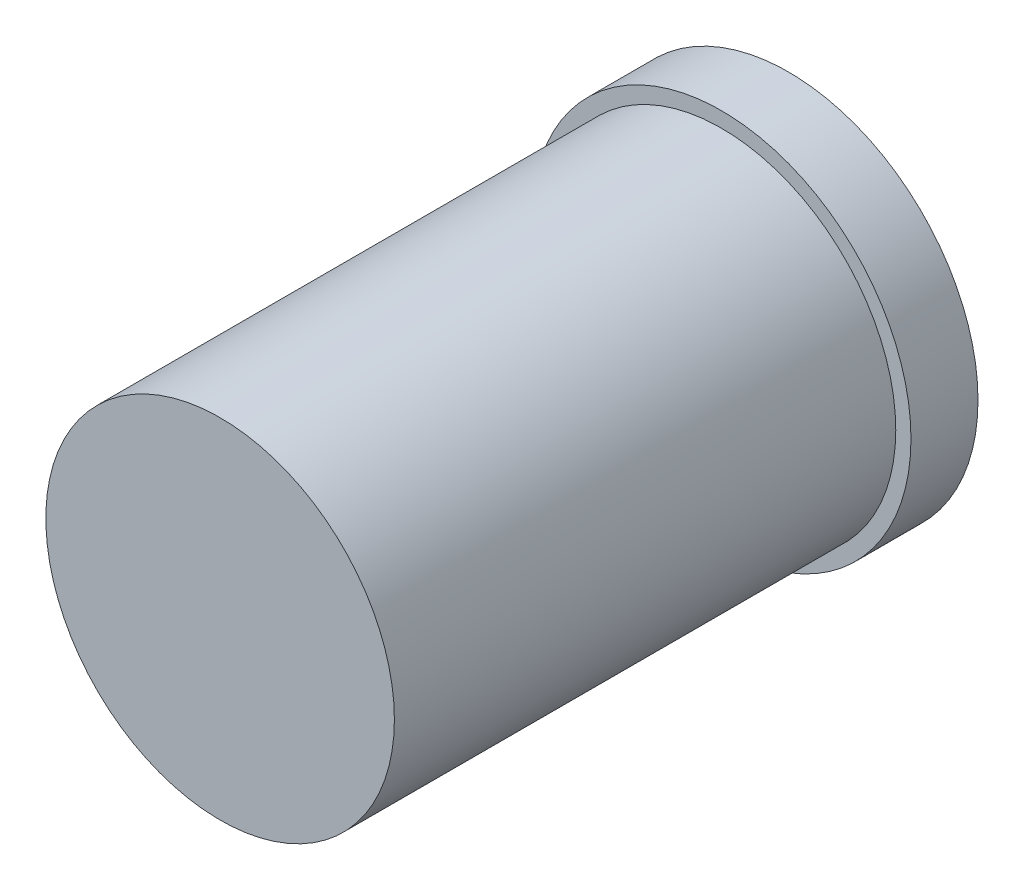
SolidWorks part; units mm, degrees
ref_plane "Front Plane" through (0, 0, 0) normal (0, 0, 1) x (1, 0, 0)
ref_plane "Top Plane" through (0, 0, 0) normal (0, 1, 0) x (1, 0, 0)
ref_plane "Right Plane" through (0, 0, 0) normal (1, 0, 0) x (0, 0, -1)
sketch "Sketch1" plane through (0, 0, 0) normal (0, 0, 1) x (1, 0, 0)
  circle A0 centre (0, 0) radius 2.4765
  dimension "D1" = 4.953
extrude "Boss-Extrude1" add sketch "Sketch1" along normal blind 7.1247
sketch "Sketch2" plane through (0, 0, 0) normal (0, 0, -1) x (-1, 0, 0)
  circle A0 centre (0, 0) radius 2.6924
  dimension "D1" = 5.3848
extrude "Boss-Extrude2" add sketch "Sketch2" along normal blind 0.9525
